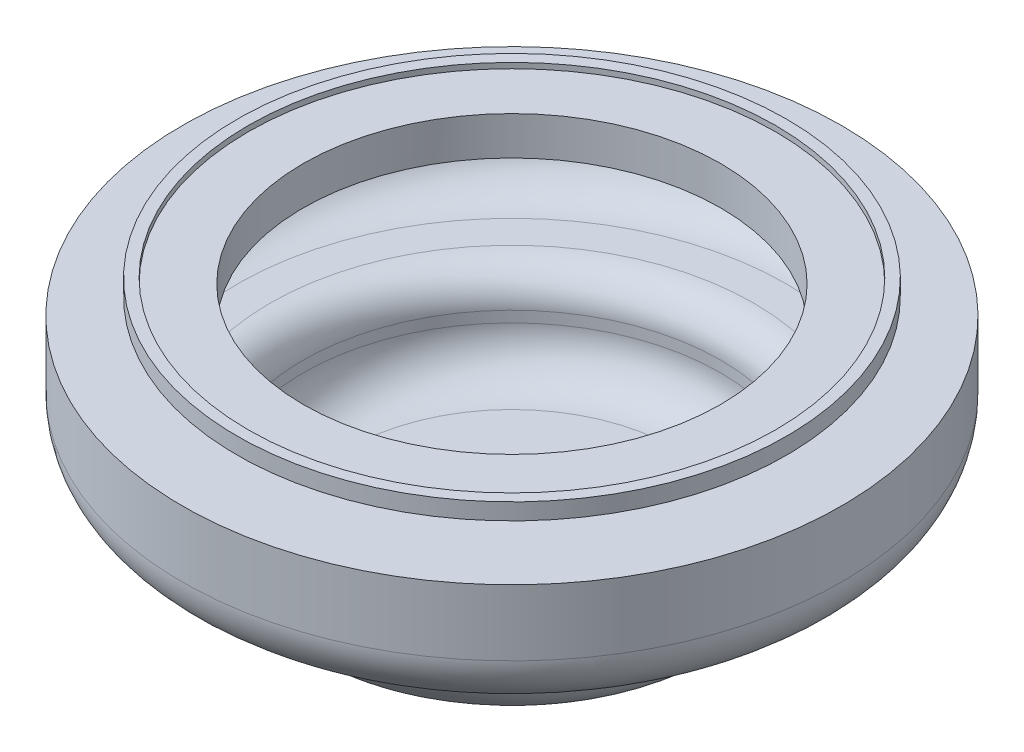
SolidWorks part; units mm, degrees
ref_plane "Front Plane" through (0, 0, 0) normal (0, 0, 1) x (1, 0, 0)
ref_plane "Top Plane" through (0, 0, 0) normal (0, 1, 0) x (1, 0, 0)
ref_plane "Right Plane" through (0, 0, 0) normal (1, 0, 0) x (0, 0, -1)
sketch "Sketch2" plane through (0, 0, 0) normal (0, 0, 1) x (1, 0, 0)
  line L0 (0, 0) -> (-25, 0)
  line L1 (-25, 0) -> (-25, -1.5)
  line L2 (-20, -1.5) -> (-20, -3)
  line L3 (-20, -3) -> (-30, -3)
  line L4 (-30, -3) -> (-30, -9)
  line L5 (-25, -1.5) -> (-20, -1.5)
  line L6 (-25, -14) -> (-22, -14)
  line L7 (-20, -16) -> (-20, -17)
  line L8 (-15, -22) -> (0, -22)
  line L9 (0, -22) -> (0, 0)
  arc A0 (-30, -9) -> (-25, -14) centre (-25, -9) ccw
  arc A1 (-20, -17) -> (-15, -22) centre (-15, -17) ccw
  arc A2 (-22, -14) -> (-20, -16) centre (-22, -16) cw
  point P15 (-20, -22)
  point P18 (-20, -14)
  dimension "D8" = 5
  dimension "D10" = 5
  dimension "D11" = 2
  dimension "D1" = 25
  dimension "D2" = 1.5
  dimension "D3" = 1.5
  dimension "D4" = 5
  dimension "D5" = 10
  dimension "D6" = 6
  dimension "D7" = 5
  dimension "D9" = 8
revolve "Revolve1" add sketch "Sketch2" angle 360 about L9
shell "Shell1" thickness 1
